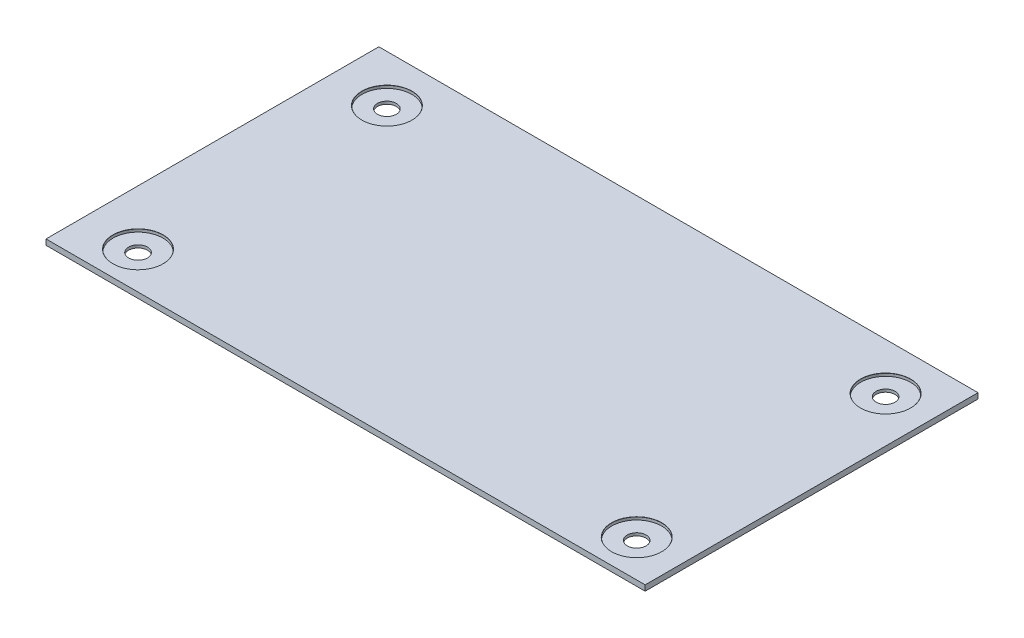
SolidWorks part; units mm, degrees
ref_plane "前视基准面" through (0, 0, 0) normal (0, 0, 1) x (1, 0, 0)
ref_plane "上视基准面" through (0, 0, 0) normal (0, 1, 0) x (1, 0, 0)
ref_plane "右视基准面" through (0, 0, 0) normal (1, 0, 0) x (0, 0, -1)
sketch "草图2" plane through (0, 0, 0) normal (0, 1, 0) x (1, 0, 0)
  line L0 (77.2555, 0) -> (-85.927, 0) construction
  line L1 (-54, 30) -> (54, 30)
  line L2 (-54, 30) -> (-54, -30)
  line L3 (-54, -30) -> (54, -30)
  line L4 (54, 30) -> (54, -30)
  line L5 (0, 77.5511) -> (0, -66.1204) construction
  dimension "D1" = 108
  dimension "D2" = 60
  dimension "D3" = 54
  dimension "D4" = 30
extrude "凸台-拉伸1" add sketch "草图2" along normal blind 1
hole_wizard "M3 六角头螺栓的柱形沉头孔1" positions "草图3" profile "草图4" counterbore size "M3" standard "GB" end condition through all
sketch "草图3" plane through (0, 1, 0) normal (0, 1, 0) x (1, 0, 0)
  point P0 (-44.085, 21.5391)
  point P2 (45.8031, 21.5391)
  point P4 (-44.085, -23.3247)
  point P6 (45.8031, -23.3247)
sketch "草图4" plane through (-44.085, 1, -21.5391) normal (1, 0, 0) x (0, 0, 1)
  line L0 (0, 0) -> (0, 1)
  line L1 (0, 1) -> (1.7, 1)
  line L3 (1.7, 1) -> (1.7, 0.5)
  line L4 (4.5, 0.5) -> (1.7, 0.5)
  line L5 (4.5, 0.5) -> (4.5, 0.025)
  line L6 (4.5, 0.025) -> (4.525, 0)
  line L7 (4.525, 0) -> (0, 0)
  line L8 (-4.5, 0.025) -> (-4.525, 0) construction
  line L11 (0, -6.35) -> (0, 107.95) construction
  dimension "通孔孔直径" = 3.4
  dimension "通孔孔深度" = 1
  dimension "柱形沉头孔直径" = 9
  dimension "柱形沉头孔深度" = 0.5
  dimension "近端锥形沉头孔直径" = 9.05
  dimension "近端锥形沉头孔角度" = 90
